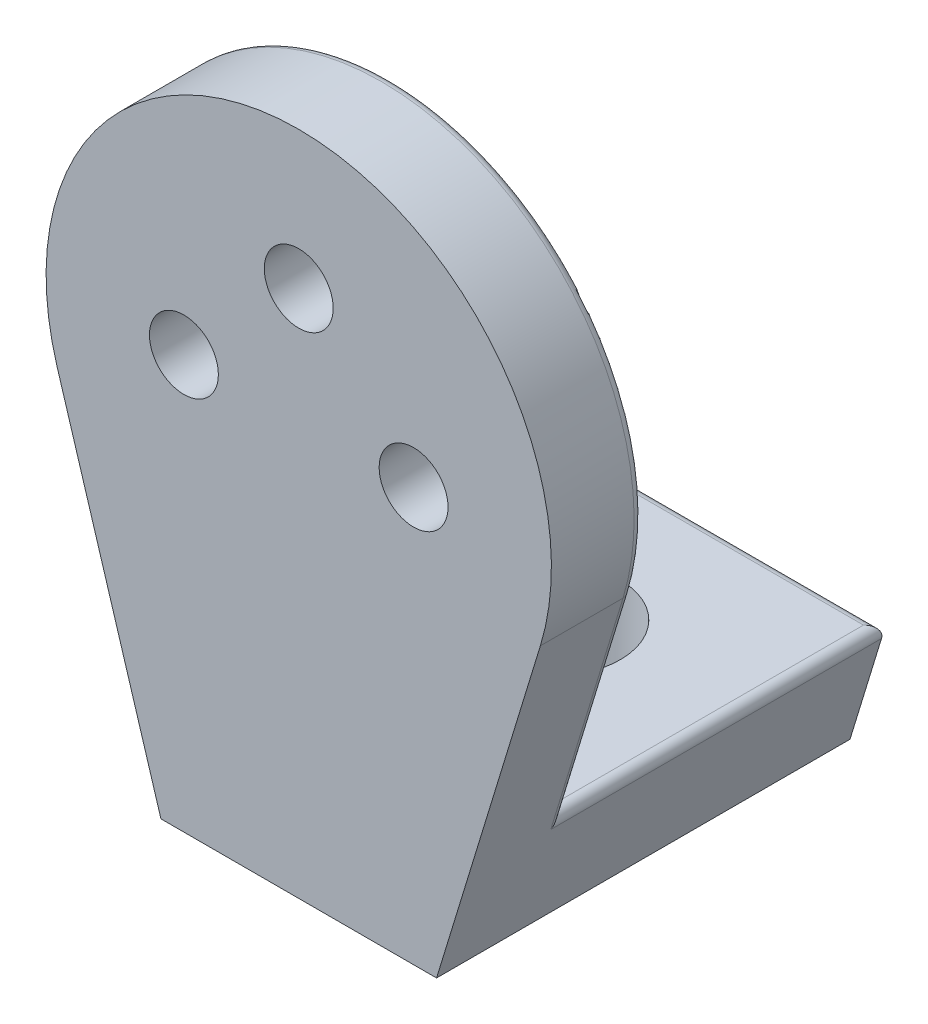
SolidWorks part; units mm, degrees
ref_plane "Front Plane" through (0, 0, 0) normal (0, 0, 1) x (1, 0, 0)
ref_plane "Top Plane" through (0, 0, 0) normal (0, 1, 0) x (1, 0, 0)
ref_plane "Right Plane" through (0, 0, 0) normal (1, 0, 0) x (0, 0, -1)
sketch "Sketch1" plane through (0, 0, 0) normal (0, 0, 1) x (1, 0, 0)
  circle A1 centre (0, 0) radius 55
  dimension "D2" = 110
extrude "Boss-Extrude1" add sketch "Sketch1" along normal blind 20
sketch "Sketch2" plane through (0, 0, 20) normal (0, 0, 1) x (1, 0, 0)
  line L0 (-52.5973, -16.0787) -> (-30, -90)
  line L1 (0, 0) -> (0, -114.253) construction
  line L2 (-30, -90) -> (30, -90)
  line L3 (52.5973, -16.0787) -> (30, -90)
  circle A0 centre (0, 0) radius 55 construction
  circle A1 centre (0, 0) radius 55
  point P9 (0, -90)
  circle M4 centre (0, 0) radius 55
  dimension "D1" = 60
  dimension "D2" = 90
extrude "Boss-Extrude2" add sketch "Sketch2" against normal up to surface (20 mm away) contours A1 L1 L2 L3 | L1 L0 L2 M4 up to face at (55, 0, 0)
sketch "Sketch3" plane through (0, 0, 0) normal (0, 0, -1) x (-1, 0, 0)
  text T0 "TforDesign" font "Century Gothic" height in points 24
extrude "Cut-Extrude1" cut sketch "Sketch3" against normal blind 1
sketch "Sketch4" plane through (0, 0, 0) normal (0, 0, -1) x (-1, 0, 0)
  line L0 (0, 0) -> (0, -12.8185) construction
  circle A0 centre (0, 25) radius 7.5
  circle A1 centre (-25, 0) radius 7.5
  circle A2 centre (25, 0) radius 7.5
  dimension "D1" = 15
  dimension "D2" = 25
  dimension "D3" = 25
extrude "Cut-Extrude2" cut sketch "Sketch4" against normal up to next
sketch "Sketch5" plane through (0, 0, 0) normal (0, 0, -1) x (-1, 0, 0)
  line L0 (-37.6423, -65) -> (37.6423, -65)
  line L3 (-52.5973, -16.0787) -> (-30, -90)
  line L4 (-30, -90) -> (30, -90)
  line L5 (30, -90) -> (52.5973, -16.0787)
  line L6 (-52.5973, -16.0787) -> (-30, -90)
  line L7 (-30, -90) -> (30, -90)
  line L8 (30, -90) -> (52.5973, -16.0787)
  arc A1 (52.5973, -16.0787) -> (-52.5973, -16.0787) centre (0, 0) ccw
  arc A2 (52.5973, -16.0787) -> (-52.5973, -16.0787) centre (0, 0) ccw
  dimension "D2" = 25
  dimension "D1" = 0
extrude "Boss-Extrude3" add sketch "Sketch5" along normal blind 70 contours L7 L8 L0 L6
sketch "Sketch6" plane through (0, -65, 0) normal (0, 1, 0) x (1, 0, 0)
  line L0 (37.6423, 70) -> (-37.6423, 0) construction
  circle A0 centre (0, 35) radius 15
  dimension "D1" = 30
extrude "Cut-Extrude3" cut sketch "Sketch6" against normal up to next
fillet "Fillet3" radius 2 6 edges at (45.1198, -40.5393, 0) (-45.1198, -40.5393, 0) (0, -65, -70) (-37.6423, -65, -35) (37.6423, -65, -35) (0, 55, 0)
